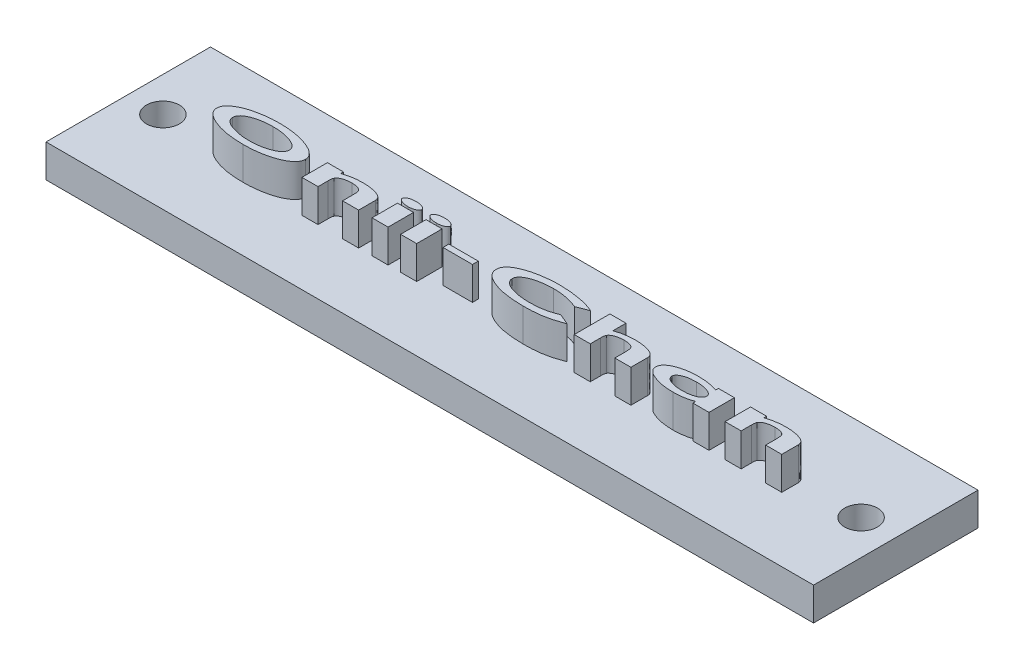
SolidWorks part; units mm, degrees
ref_plane "Front Plane" through (0, 0, 0) normal (0, 0, 1) x (1, 0, 0)
ref_plane "Top Plane" through (0, 0, 0) normal (0, 1, 0) x (1, 0, 0)
ref_plane "Right Plane" through (0, 0, 0) normal (1, 0, 0) x (0, 0, -1)
sketch "Sketch3" plane through (0, 0, 0) normal (0, 1, 0) x (1, 0, 0)
  line L0 (0, -7.5) -> (0, 7.5)
  line L1 (-35, 7.5) -> (35, 7.5)
  line L2 (-35, 7.5) -> (-35, -7.5)
  line L3 (-35, -7.5) -> (35, -7.5)
  line L4 (35, 7.5) -> (35, -7.5)
  line L5 (-35, 7.5) -> (35, -7.5) construction
  line L6 (-35, -7.5) -> (35, 7.5) construction
  line L7 (-35, 0) -> (35, 0)
  point P0 (0, 0)
  point P9 (0, 0)
  point P12 (0, 0)
  dimension "D1" = 15
  dimension "D3" = 70
extrude "Boss-Extrude2" add sketch "Sketch3" along normal blind 3
sketch "Sketch4" plane through (0, 3, 0) normal (0, 1, 0) x (1, 0, 0)
  text T0 "<b>Onii-Chan</b>" font "Century Gothic" height 3.175
extrude "Boss-Extrude3" add sketch "Sketch4" along normal blind 3
sketch "Sketch6" plane through (0, 3, 0) normal (0, 1, 0) x (1, 0, 0)
  line L0 (0, 7.5) -> (0, -7.5)
  line L1 (-35, 7.5) -> (35, 7.5)
  line L2 (-35, 7.5) -> (-35, -7.5)
  line L3 (-35, -7.5) -> (35, -7.5)
  line L4 (35, 7.5) -> (35, -7.5)
  line L5 (-35, 0) -> (35, 0)
  circle A0 centre (-31.837, 0) radius 1.5
  circle A2 centre (31.837, 0) radius 1.5
extrude "Cut-Extrude1" cut sketch "Sketch6" against normal blind 3 contours L5 A0 | L5 A0 | A2 L5 | A2 L5
